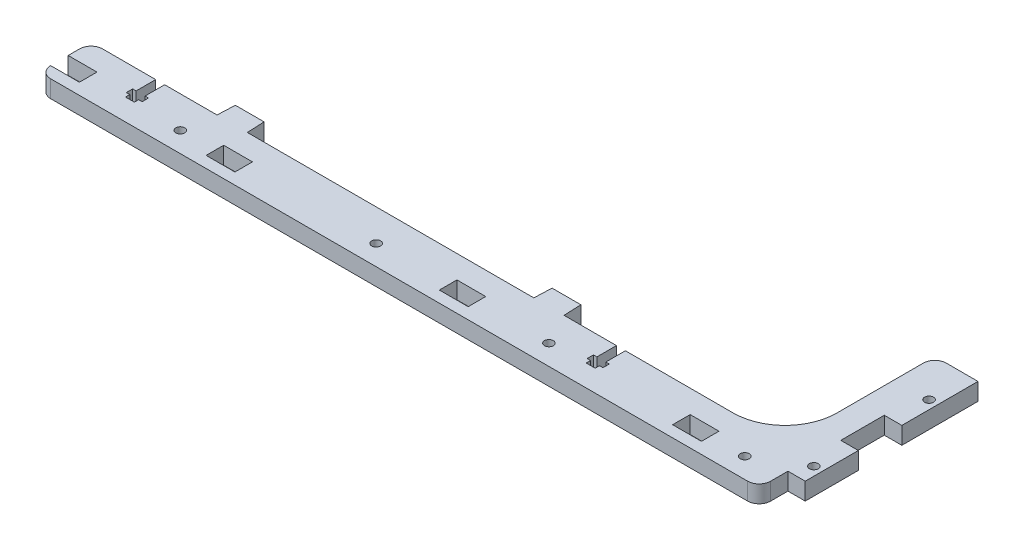
SolidWorks part; units mm, degrees
ref_plane "Спереди" through (0, 0, 0) normal (0, 0, 1) x (1, 0, 0)
ref_plane "Сверху" through (0, 0, 0) normal (0, 1, 0) x (1, 0, 0)
ref_plane "Справа" through (0, 0, 0) normal (1, 0, 0) x (0, 0, -1)
sketch "Эскиз1" plane through (0, 0, 0) normal (0, 1, 0) x (1, 0, 0)
  line L0 (-94.559, -25.1195) -> (-84.559, -25.1195)
  line L1 (-84.559, -25.1195) -> (-84.559, -19.0195)
  line L2 (-84.559, -19.0195) -> (-94.559, -19.0195)
  line L3 (-94.559, -19.0195) -> (-94.559, -25.1195)
  line L4 (77.441, -25.1195) -> (77.441, -19.0195)
  line L5 (77.441, -19.0195) -> (67.441, -19.0195)
  line L6 (67.441, -19.0195) -> (67.441, -25.1195)
  line L7 (67.441, -25.1195) -> (77.441, -25.1195)
  line L8 (-3.559, -25.1195) -> (-3.559, -19.0195)
  line L9 (-3.559, -19.0195) -> (-13.559, -19.0195)
  line L10 (-13.559, -19.0195) -> (-13.559, -25.1195)
  line L11 (-13.559, -25.1195) -> (-3.559, -25.1195)
  line L12 (33.891, -17.8695) -> (32.691, -17.8695)
  line L13 (32.691, -17.8695) -> (32.691, -20.0695)
  line L14 (32.691, -20.0695) -> (33.891, -20.0695)
  line L15 (33.891, -20.0695) -> (33.891, -21.5695)
  line L16 (33.891, -21.5695) -> (36.991, -21.5695)
  line L17 (36.991, -21.5695) -> (36.991, -20.0695)
  line L18 (36.991, -20.0695) -> (38.191, -20.0695)
  line L19 (38.191, -20.0695) -> (38.191, -17.8695)
  line L20 (38.191, -17.8695) -> (36.991, -17.8695)
  line L21 (36.991, -17.8695) -> (36.991, -11.0695)
  line L22 (74.441, -11.0695) -> (36.991, -11.0695)
  line L23 (92.441, 36.9305) -> (92.441, 6.9305)
  line L24 (107.441, 40.9305) -> (96.441, 40.9305)
  line L25 (107.441, 14.4805) -> (107.441, 40.9305)
  line L26 (107.441, 14.4805) -> (101.341, 14.4805)
  line L27 (101.341, 14.4805) -> (101.341, -0.6195)
  line L28 (101.341, -0.6195) -> (107.441, -0.6195)
  line L29 (101.441, -19.0695) -> (107.441, -19.0695)
  line L30 (101.441, -25.0695) -> (101.441, -19.0695)
  line L31 (-144.5593, -29.0695) -> (97.441, -29.0695)
  line L32 (-138.559, -25.1195) -> (-148.559, -25.1195)
  line L33 (-138.559, -19.0195) -> (-138.559, -25.1195)
  line L34 (-148.559, -19.0195) -> (-138.559, -19.0195)
  line L35 (-148.559, -15.0695) -> (-148.559, -19.0195)
  line L36 (-126.109, -11.0695) -> (-144.559, -11.0695)
  line L37 (-126.109, -11.0695) -> (-126.109, -17.8695)
  line L38 (-126.109, -17.8695) -> (-127.309, -17.8695)
  line L39 (-127.309, -17.8695) -> (-127.309, -20.0695)
  line L40 (-127.309, -20.0695) -> (-126.109, -20.0695)
  line L41 (-126.109, -20.0695) -> (-126.109, -21.5695)
  line L42 (-126.109, -21.5695) -> (-123.009, -21.5695)
  line L43 (-123.009, -21.5695) -> (-123.009, -20.0695)
  line L44 (-123.009, -20.0695) -> (-121.809, -20.0695)
  line L45 (-121.809, -20.0695) -> (-121.809, -17.8695)
  line L46 (-121.809, -17.8695) -> (-123.009, -17.8695)
  line L47 (-123.009, -17.8695) -> (-123.009, -11.0695)
  line L48 (-104.559, -4.9695) -> (-104.809, -11.0695)
  line L49 (-94.559, -4.9695) -> (-104.559, -4.9695)
  line L50 (-94.309, -11.0695) -> (-94.559, -4.9695)
  line L51 (5.191, -11.0695) -> (-94.309, -11.0695)
  line L52 (5.441, -4.9695) -> (5.191, -11.0695)
  line L53 (15.441, -4.9695) -> (5.441, -4.9695)
  line L54 (15.691, -11.0695) -> (15.441, -4.9695)
  line L55 (33.891, -11.0695) -> (33.891, -17.8695)
  line L56 (107.441, -19.0695) -> (107.441, -0.6195)
  line L57 (-104.809, -11.0695) -> (-123.009, -11.0695)
  line L58 (33.891, -11.0695) -> (15.691, -11.0695)
  circle A0 centre (104.441, 26.9305) radius 1.55
  circle A1 centre (104.441, -13.0695) radius 1.55
  circle A2 centre (-106.559, -22.0695) radius 1.55
  circle A3 centre (-38.559, -22.0695) radius 1.55
  circle A4 centre (21.441, -22.0695) radius 1.55
  circle A5 centre (89.441, -22.0695) radius 1.55
  arc A6 (74.441, -11.0695) -> (92.441, 6.9305) centre (74.441, 6.9305) ccw
  arc A7 (96.441, 40.9305) -> (92.441, 36.9305) centre (96.441, 36.9305) ccw
  arc A8 (97.441, -29.0695) -> (101.441, -25.0695) centre (97.441, -25.0695) ccw
  arc A9 (-148.559, -25.1195) -> (-144.5593, -29.0695) centre (-144.5593, -25.0695) ccw
  arc A10 (-144.559, -11.0695) -> (-148.559, -15.0695) centre (-144.559, -15.0695) ccw
extrude "Бобышка-Вытянуть1" add sketch "Эскиз1" along normal blind 6
